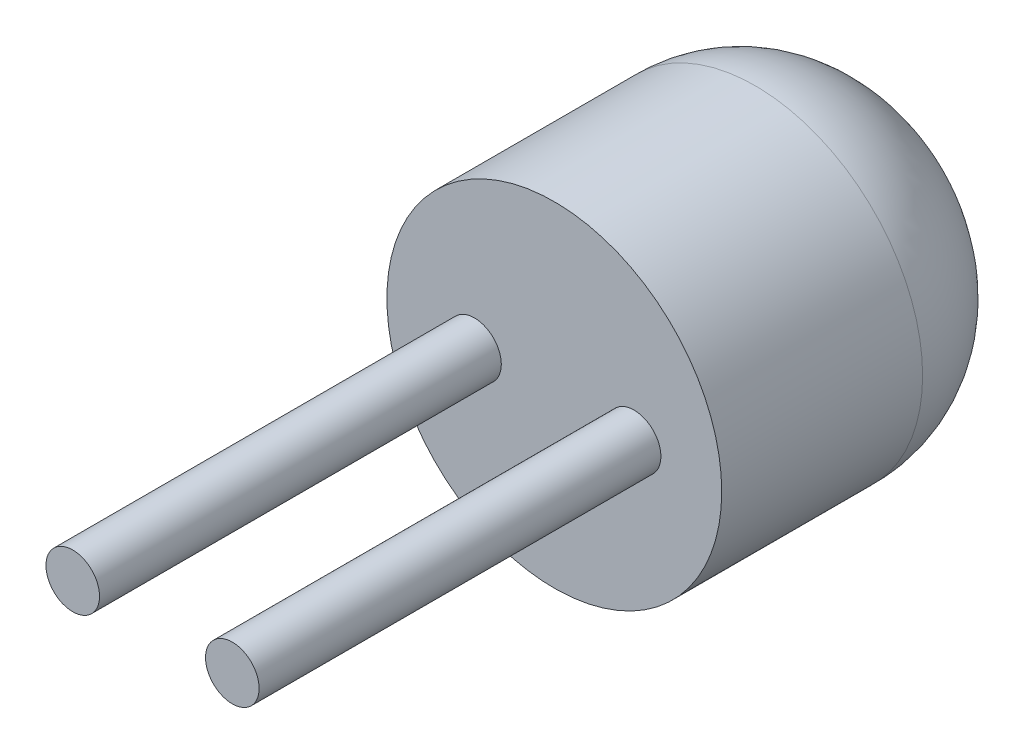
SolidWorks part; units mm, degrees
ref_plane "Front Plane" through (0, 0, 0) normal (0, 0, 1) x (1, 0, 0)
ref_plane "Top Plane" through (0, 0, 0) normal (0, 1, 0) x (1, 0, 0)
ref_plane "Right Plane" through (0, 0, 0) normal (1, 0, 0) x (0, 0, -1)
sketch "Sketch1" plane through (0, 0, 0) normal (0, 0, 1) x (1, 0, 0)
  circle A0 centre (-53, 47) radius 2.5
extrude "Boss-Extrude1" add sketch "Sketch1" against normal blind 5
sketch "Sketch2" plane through (0, 0, 0) normal (0, 0, 1) x (1, 0, 0)
  line L0 (-55.5, 47) -> (-50.5, 47) construction
  line L1 (-53, 47) -> (-53, 49.5) construction
  circle A0 centre (-53, 47) radius 2.5 construction
  circle A1 centre (-54.1916, 47) radius 0.4
  circle A2 centre (-51.8084, 47) radius 0.4
extrude "Boss-Extrude2" add sketch "Sketch2" along normal blind 6
fillet "Fillet1" radius 2 1 edges at (-50.5, 47, -5)
